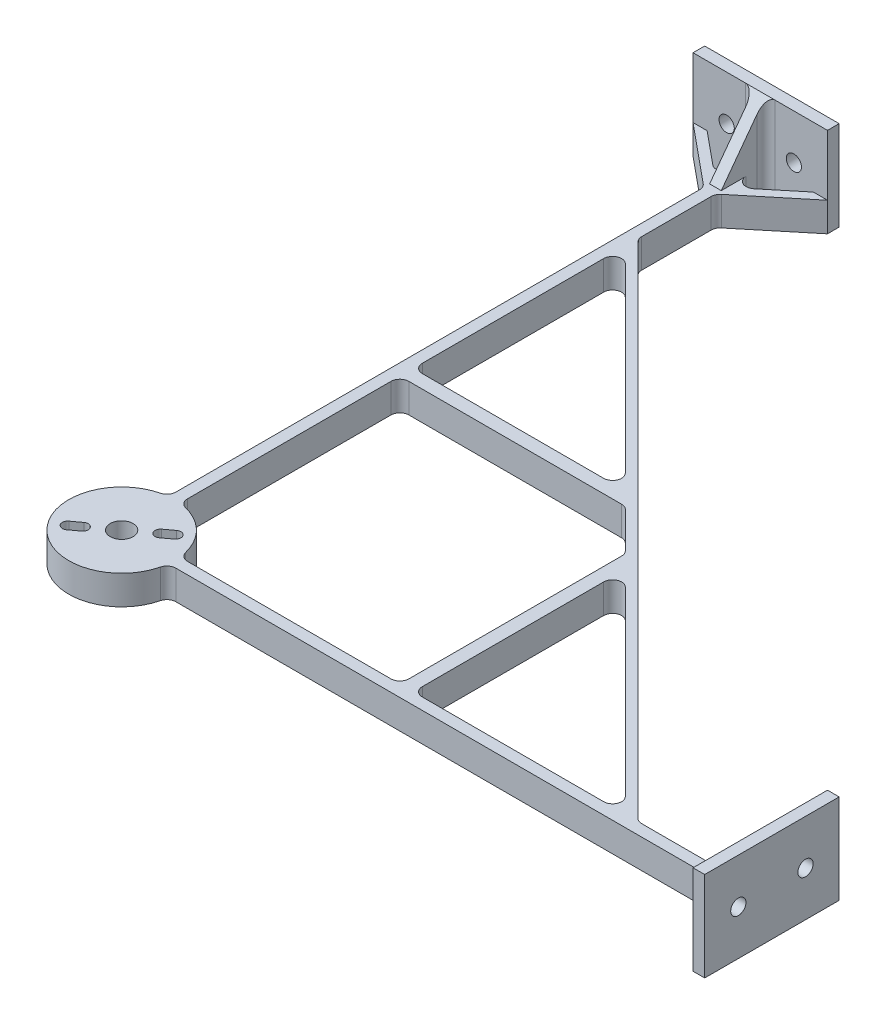
SolidWorks part; units mm, degrees
ref_plane "Front Plane" through (0, 0, 0) normal (0, 0, 1) x (1, 0, 0)
ref_plane "Top Plane" through (0, 0, 0) normal (0, 1, 0) x (1, 0, 0)
ref_plane "Right Plane" through (0, 0, 0) normal (1, 0, 0) x (0, 0, -1)
sketch "Sketch1" plane through (0, 0, 0) normal (0, 1, 0) x (1, 0, 0)
  line L0 (1.651, 14.8948) -> (1.651, 77.2021)
  line L1 (0, 0) -> (0, 189.2633) construction
  line L2 (-1.651, 14.8948) -> (-1.651, 180.975)
  line L3 (-1.651, 180.975) -> (1.651, 180.975)
  line L4 (-16.663, -12.33) -> (16.2408, 12.0176) construction
  line L5 (14.8948, -1.651) -> (180.975, -1.651)
  line L6 (6.3296, 4.6836) -> (8.7797, 6.4967) construction
  line L7 (5.4231, 5.9087) -> (7.8732, 7.7217)
  line L8 (180.975, -1.651) -> (180.975, 1.651)
  line L9 (14.8948, 1.651) -> (141.0789, 1.651)
  line L10 (7.2361, 3.4586) -> (9.6862, 5.2716)
  line L11 (0, 0) -> (12.0155, -16.238) construction
  line L12 (-6.3296, -4.6836) -> (-8.7797, -6.4967) construction
  line L13 (-7.2361, -3.4586) -> (-9.6862, -5.2716)
  line L14 (-5.4231, -5.9087) -> (-7.8732, -7.7217)
  line L15 (-1.651, 14.8948) -> (14.8948, -1.651) construction
  line L16 (1.651, 141.0789) -> (61.7178, 81.0121)
  line L17 (144.6711, 1.651) -> (1.651, 144.6711)
  line L18 (144.6711, 1.651) -> (166.629, 1.651)
  line L19 (141.0789, 1.651) -> (144.6711, 1.651) construction
  line L20 (1.651, 144.6711) -> (1.651, 180.975)
  line L21 (1.651, 81.0121) -> (61.7178, 81.0121)
  line L22 (1.651, 77.2021) -> (65.5278, 77.2021)
  line L23 (0, 0) -> (69.7604, 69.7604) construction
  line L24 (77.2021, 1.651) -> (77.2021, 65.5278)
  line L25 (81.0121, 1.651) -> (81.0121, 61.7178)
  line L26 (81.0121, 61.7178) -> (141.0789, 1.651)
  line L27 (65.5278, 77.2021) -> (77.2021, 65.5278)
  line L28 (1.651, 81.0121) -> (1.651, 141.0789)
  line L29 (169.921, 1.651) -> (180.975, 15.0573)
  line L30 (180.975, 15.0573) -> (180.975, 19.05)
  line L31 (180.975, 19.05) -> (166.629, 1.651)
  line L32 (166.4345, 0) -> (201.9953, 0) construction
  line L33 (180.975, -19.05) -> (166.629, -1.651)
  line L34 (180.975, -15.0573) -> (180.975, -19.05)
  line L35 (169.921, -1.651) -> (180.975, -15.0573)
  line L36 (169.921, 1.651) -> (180.975, 1.651)
  line L37 (166.629, 1.651) -> (169.921, 1.651) construction
  line L38 (-15.0573, 180.975) -> (-19.05, 180.975)
  line L39 (-19.05, 180.975) -> (-1.651, 166.629)
  line L40 (-1.651, 169.921) -> (-15.0573, 180.975)
  line L41 (1.651, 169.921) -> (15.0573, 180.975)
  line L42 (15.0573, 180.975) -> (19.05, 180.975)
  line L43 (19.05, 180.975) -> (1.651, 166.629)
  arc A0 (14.8948, 1.651) -> (1.651, 14.8948) centre (0, 0) ccw
  circle A1 centre (0, 0) radius 3.2385
  arc A2 (5.4231, 5.9087) -> (7.2361, 3.4586) centre (6.3296, 4.6836) ccw
  arc A3 (9.6862, 5.2716) -> (7.8732, 7.7217) centre (8.7797, 6.4967) ccw
  arc A4 (-7.2361, -3.4586) -> (-5.4231, -5.9087) centre (-6.3296, -4.6836) cw
  arc A5 (-7.8732, -7.7217) -> (-9.6862, -5.2716) centre (-8.7797, -6.4967) cw
  arc A6 (-1.651, 14.8948) -> (14.8948, -1.651) centre (0, 0) ccw
  point P14 (7.5546, 5.5901)
  point P25 (-7.5546, -5.5901)
  point P34 (142.875, 1.651)
  point P53 (168.275, 1.651)
  dimension "D3" = 29.972
  dimension "D1" = 6.477
  dimension "D6" = 1.524
  dimension "D7" = 3.048
  dimension "D2" = 53.5
  dimension "D4" = 3.302
  dimension "D5" = 3.302
  dimension "D8" = 7.874
  dimension "D9" = 2.54
  dimension "D10" = 38.1
  dimension "D11" = 3.81
  dimension "D12" = 16.51
  dimension "D13" = 38.1
  dimension "D14" = 12.7
  dimension "D15" = 2.54
  dimension "D16" = 180.975
  dimension "D17" = 180.975
extrude "Boss-Extrude1" add sketch "Sketch1" along normal blind 8.255
sketch "Sketch3" plane through (0, 0, 0) normal (0, 1, 0) x (1, 0, 0)
  line L0 (0, 0) -> (128.7769, 128.7769) construction
  line L1 (180.975, 19.05) -> (184.277, 19.05)
  line L2 (180.975, 19.05) -> (180.975, -19.05)
  line L3 (180.975, -19.05) -> (184.277, -19.05)
  line L4 (184.277, 19.05) -> (184.277, -19.05)
  line L5 (19.05, 184.277) -> (-19.05, 184.277)
  line L6 (-19.05, 180.975) -> (-19.05, 184.277)
  line L7 (19.05, 180.975) -> (-19.05, 180.975)
  line L8 (19.05, 180.975) -> (19.05, 184.277)
  dimension "D1" = 3.302
extrude "Boss-Extrude3" add sketch "Sketch3" along normal blind 25.4
sketch "Sketch4" plane through (0, 8.255, 0) normal (0, 1, 0) x (1, 0, 0)
  line L0 (65.2584, 81.0637) -> (64.3604, 80.1656)
  line L1 (144.6711, 1.651) -> (1.651, 144.6711) construction
  line L2 (64.3604, 80.1656) -> (80.1656, 64.3604)
  line L3 (80.1656, 64.3604) -> (81.0637, 65.2584)
  line L4 (81.0637, 65.2584) -> (65.2584, 81.0637)
  line L5 (71.365, 71.365) -> (72.263, 72.263) construction
  line L6 (65.5278, 77.2021) -> (77.2021, 65.5278) construction
  dimension "D1" = 22.352
  dimension "D2" = 1.27
extrude "Boss-Extrude4" [suppressed] add sketch "Sketch4" along normal blind 11.938
sketch "Sketch5" plane through (184.277, 0, 0) normal (1, 0, 0) x (0, 0, -1)
  line L0 (-19.05, 25.4) -> (19.05, 25.4) construction
  line L3 (0, 4.9298) -> (0, 30.0782) construction
  circle A0 centre (-9.525, 12.7) radius 2.159
  circle A1 centre (9.525, 12.7) radius 2.159
  dimension "D1" = 4.318
  dimension "D2" = 19.05
  dimension "D3" = 12.7
ref_plane "Plane1" [suppressed] through (0, 0, 0) normal (0.7071, 0, 0.7071) x (0.7071, 0, -0.7071)
extrude "Cut-Extrude1" cut sketch "Sketch5" against normal through all
mirror "Mirror1" about plane through (0, 0, 0) normal (0.7071, 0, 0.7071) of "Cut-Extrude1"
sketch "Sketch6" plane through (0, 0, 0) normal (0, 1, 0) x (1, 0, 0)
  line L0 (169.921, 1.651) -> (180.975, 1.651) construction
  line L1 (180.975, -1.651) -> (168.275, -1.651)
  line L2 (180.975, -1.651) -> (180.975, 1.651)
  line L3 (180.975, 1.651) -> (168.275, 1.651)
  line L4 (168.275, -1.651) -> (168.275, 1.651)
  dimension "D1" = 12.7
extrude "Boss-Extrude5" add sketch "Sketch6" along normal blind 25.4
sketch "Sketch7" plane through (0, 0, -1.651) normal (0, 0, -1) x (-1, 0, 0)
  line L0 (-180.975, 25.4) -> (-168.275, 8.255)
  line L1 (-168.275, 8.255) -> (-168.275, 25.4)
  line L2 (-168.275, 25.4) -> (-180.975, 25.4)
extrude "Cut-Extrude2" cut sketch "Sketch7" against normal blind 25.4
sketch "Sketch8" plane through (0, 0, 0) normal (0, 1, 0) x (1, 0, 0)
  line L0 (1.651, 169.921) -> (1.651, 180.975) construction
  line L1 (-1.651, 180.975) -> (1.651, 180.975)
  line L2 (-1.651, 180.975) -> (-1.651, 168.275)
  line L3 (-1.651, 168.275) -> (1.651, 168.275)
  line L4 (1.651, 180.975) -> (1.651, 168.275)
  dimension "D1" = 12.7
extrude "Boss-Extrude6" add sketch "Sketch8" along normal blind 25.4
sketch "Sketch9" plane through (1.651, 0, 0) normal (1, 0, 0) x (0, 0, -1)
  line L0 (180.975, 25.4) -> (168.275, 8.255)
  line L1 (168.275, 8.255) -> (168.275, 25.4)
  line L2 (168.275, 25.4) -> (180.975, 25.4)
extrude "Cut-Extrude3" cut sketch "Sketch9" against normal blind 25.4
fillet "Fillet1" radius 2.54 28 edges at (180.975, 12.7, 1.651) (-1.651, 12.7, -180.975) (141.0789, 4.1275, -1.651) (61.7178, 4.1275, -81.0121) (1.651, 4.1275, -141.0789) (81.0121, 4.1275, -61.7178) (14.8948, 4.1275, 1.651) (-1.651, 4.1275, -14.8948) (180.975, 12.7, -1.651) (77.2021, 4.1275, -1.651) (1.651, 12.7, -180.975) (1.651, 4.1275, -77.2021) (166.629, 4.1275, 1.651) (65.5278, 4.1275, -77.2021) (-1.651, 4.1275, -166.629) (77.2021, 4.1275, -65.5278) (1.651, 4.1275, -166.629) (1.651, 4.1275, -14.8948) (1.651, 4.1275, -144.6711) (1.651, 4.1275, -81.0121) (81.0121, 4.1275, -1.651) (166.629, 4.1275, -1.651) (14.8948, 4.1275, -1.651) (144.6711, 4.1275, -1.651) (-1.651, 4.1275, -169.921) (1.651, 4.1275, -169.921) (169.921, 4.1275, 1.651) (169.921, 4.1275, -1.651)
